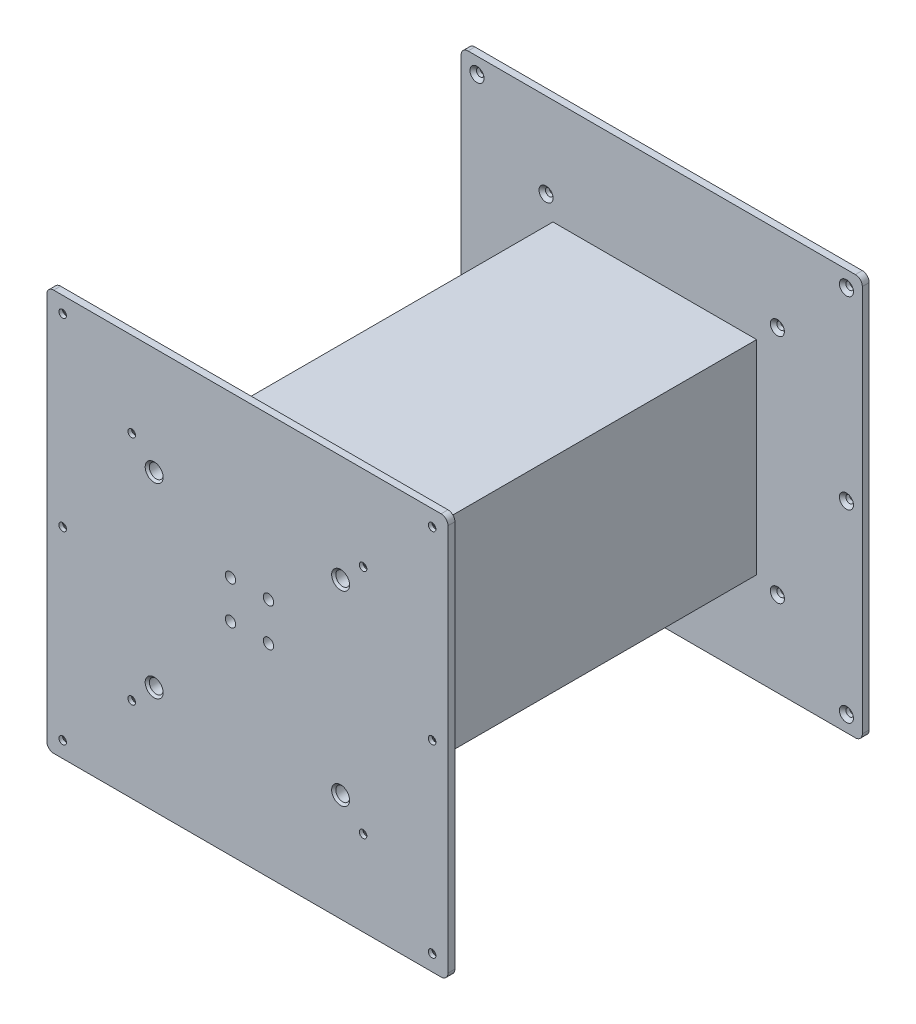
SolidWorks part; units mm, degrees
ref_plane "Front Plane" through (0, 0, 0) normal (0, 0, 1) x (1, 0, 0)
ref_plane "Top Plane" through (0, 0, 0) normal (0, 1, 0) x (1, 0, 0)
ref_plane "Right Plane" through (0, 0, 0) normal (1, 0, 0) x (0, 0, -1)
sketch "Sketch1" plane through (0, 0, 0) normal (0, 0, 1) x (1, 0, 0)
  line L1 (-147.574, 147.574) -> (147.574, 147.574)
  line L2 (-147.574, 147.574) -> (-147.574, -147.574)
  line L3 (-147.574, -147.574) -> (147.574, -147.574)
  line L4 (147.574, 147.574) -> (147.574, -147.574)
  line L5 (-147.574, 147.574) -> (147.574, -147.574) construction
  line L6 (-147.574, -147.574) -> (147.574, 147.574) construction
  point P0 (0, 0)
  dimension "D1" = 295.148
  dimension "D2" = 295.148
extrude "Boss-Extrude1" add sketch "Sketch1" along normal blind 5.08
sketch "Sketch2" plane through (0, 0, 5.08) normal (0, 0, 1) x (1, 0, 0)
  line L1 (-69.596, 69.596) -> (69.596, 69.596)
  line L2 (-69.596, 69.596) -> (-69.596, -69.596)
  line L3 (-69.596, -69.596) -> (69.596, -69.596)
  line L4 (69.596, 69.596) -> (69.596, -69.596)
  line L5 (-69.596, 69.596) -> (69.596, -69.596) construction
  line L6 (-69.596, -69.596) -> (69.596, 69.596) construction
  point P0 (0, 0)
  dimension "D1" = 139.192
  dimension "D2" = 139.192
extrude "Boss-Extrude2" add sketch "Sketch2" along normal blind 5.08
sketch "Sketch3" plane through (0, 0, 10.16) normal (0, 0, 1) x (1, 0, 0)
  line L1 (-74.93, 74.93) -> (74.93, 74.93)
  line L2 (-74.93, 74.93) -> (-74.93, -74.93)
  line L3 (-74.93, -74.93) -> (74.93, -74.93)
  line L4 (74.93, 74.93) -> (74.93, -74.93)
  line L5 (-74.93, 74.93) -> (74.93, -74.93) construction
  line L6 (-74.93, -74.93) -> (74.93, 74.93) construction
  point P0 (0, 0)
  dimension "D1" = 149.86
  dimension "D2" = 149.86
extrude "Boss-Extrude3" add sketch "Sketch3" along normal blind 294.64
sketch "Sketch4" plane through (0, 0, 304.8) normal (0, 0, 1) x (1, 0, 0)
  line L1 (147.574, -147.574) -> (-147.574, -147.574)
  line L2 (147.574, -147.574) -> (147.574, 147.574)
  line L3 (147.574, 147.574) -> (-147.574, 147.574)
  line L4 (-147.574, -147.574) -> (-147.574, 147.574)
  line L5 (147.574, -147.574) -> (-147.574, 147.574) construction
  line L6 (147.574, 147.574) -> (-147.574, -147.574) construction
  point P0 (0, 0)
extrude "Boss-Extrude4" add sketch "Sketch4" along normal blind 5.08
sketch "Sketch5" plane through (0, 0, 0) normal (0, 0, -1) x (-1, 0, 0)
  line L0 (147.574, -147.574) -> (-147.574, -147.574) construction
  line L1 (-147.574, -147.574) -> (-147.574, 147.574) construction
  line L2 (-147.574, 147.574) -> (147.574, 147.574) construction
  circle A0 centre (-135.89, 135.89) radius 2.794
  circle A1 centre (135.89, 135.89) radius 2.794
  circle A2 centre (135.89, -135.89) radius 2.794
  circle A3 centre (-135.89, -135.89) radius 2.794
  circle A4 centre (-135.89, 0) radius 2.794
  circle A5 centre (135.89, 0) radius 2.794
  circle A6 centre (-85.09, 85.09) radius 2.794
  circle A7 centre (85.09, 85.09) radius 2.794
  circle A8 centre (85.09, -85.09) radius 2.794
  circle A9 centre (-85.09, -85.09) radius 2.794
  dimension "D1" = 271.78
  dimension "D2" = 271.78
  dimension "D3" = 11.684
  dimension "D4" = 11.684
  dimension "D5" = 271.78
  dimension "D6" = 271.78
  dimension "D7" = 5.588
  dimension "D8" = 5.588
  dimension "D9" = 5.588
  dimension "D10" = 5.588
  dimension "D11" = 5.588
  dimension "D12" = 5.588
  dimension "D13" = 170.18
  dimension "D14" = 170.18
  dimension "D15" = 170.18
  dimension "D16" = 62.484
  dimension "D17" = 62.484
  dimension "D18" = 5.588
  dimension "D19" = 5.588
  dimension "D20" = 5.588
  dimension "D21" = 5.588
extrude "Cut-Extrude1" cut sketch "Sketch5" against normal through all
chamfer "Chamfer1" distance 2.38 angle 45 1 edges at (138.684, 135.89, 304.8)
chamfer "Chamfer2" distance 2.38 angle 45 19 edges at (138.684, 0, 5.08) (138.684, -135.89, 5.08) (87.884, -85.09, 5.08) (-133.096, -135.89, 5.08) (-82.296, -85.09, 5.08) (-133.096, 0, 5.08) (-133.096, 0, 304.8) (-133.096, -135.89, 304.8) (-82.296, -85.09, 304.8) (138.684, 135.89, 5.08) (87.884, 85.09, 5.08) (-82.296, 85.09, 5.08) (-133.096, 135.89, 5.08) (-82.296, 85.09, 304.8) (-133.096, 135.89, 304.8) (87.884, -85.09, 304.8) (138.684, -135.89, 304.8) (138.684, 0, 304.8) (87.884, 85.09, 304.8)
fillet "Fillet1" radius 5.08 1 edges at (147.574, 147.574, 2.54)
fillet "Fillet2" radius 5.08 7 edges at (147.574, 147.574, 307.34) (147.574, -147.574, 2.54) (147.574, -147.574, 307.34) (-147.574, -147.574, 2.54) (-147.574, -147.574, 307.34) (-147.574, 147.574, 307.34) (-147.574, 147.574, 2.54)
sketch "Sketch6" plane through (0, 0, 309.88) normal (0, 0, 1) x (1, 0, 0)
  line L0 (142.494, 147.574) -> (-142.494, 147.574) construction
  line L1 (-147.574, 142.494) -> (-147.574, -142.494) construction
  circle A0 centre (-68.58, -68.58) radius 5.08
  circle A1 centre (-68.58, 68.58) radius 5.08
  circle A2 centre (68.58, 68.58) radius 5.08
  circle A3 centre (68.58, -68.58) radius 5.08
  dimension "D1" = 137.16
  dimension "D2" = 137.16
  dimension "D3" = 137.16
  dimension "D4" = 78.994
  dimension "D5" = 10.16
  dimension "D6" = 10.16
  dimension "D7" = 10.16
  dimension "D8" = 10.16
  dimension "D9" = 78.994
extrude "Cut-Extrude3" cut sketch "Sketch6" against normal blind 35.56
chamfer "Chamfer3" distance 1.524 angle 45 4 edges at (73.66, 68.58, 309.88) (-63.5, -68.58, 309.88) (-63.5, 68.58, 309.88) (73.66, -68.58, 309.88)
sketch "Sketch7" plane through (0, 0, 0) normal (0, 0, -1) x (-1, 0, 0)
  line L0 (-142.494, 147.574) -> (142.494, 147.574) construction
  line L1 (-147.574, -142.494) -> (-147.574, 142.494) construction
  circle A0 centre (-53.34, 53.34) radius 5.08
  circle A1 centre (-53.34, -53.34) radius 5.08
  circle A2 centre (53.34, -53.34) radius 5.08
  circle A3 centre (53.34, 53.34) radius 5.08
  dimension "D1" = 106.68
  dimension "D2" = 106.68
  dimension "D3" = 106.68
  dimension "D4" = 94.234
  dimension "D5" = 94.234
  dimension "D6" = 10.16
  dimension "D7" = 10.16
  dimension "D8" = 10.16
  dimension "D9" = 10.16
extrude "Cut-Extrude4" cut sketch "Sketch7" against normal blind 35.56
chamfer "Chamfer5" distance 1.524 angle 45 4 edges at (48.26, -53.34, 0) (-58.42, -53.34, 0) (-58.42, 53.34, 0) (48.26, 53.34, 0)
sketch "Sketch8" plane through (0, 0, 309.88) normal (0, 0, 1) x (1, 0, 0)
  line L0 (142.494, 147.574) -> (-142.494, 147.574) construction
  line L1 (147.574, -142.494) -> (147.574, 142.494) construction
  circle A0 centre (15.494, 29.464) radius 3.81
  circle A1 centre (15.494, 1.524) radius 3.81
  circle A2 centre (-12.446, 1.524) radius 3.81
  circle A3 centre (-12.446, 29.464) radius 3.81
  dimension "D1" = 27.94
  dimension "D2" = 27.94
  dimension "D3" = 118.11
  dimension "D4" = 118.11
  dimension "D5" = 7.62
  dimension "D6" = 7.62
  dimension "D7" = 7.62
  dimension "D8" = 7.62
  dimension "D9" = 132.08
  dimension "D10" = 27.94
extrude "Cut-Extrude5" cut sketch "Sketch8" against normal blind 35.56
sketch "Sketch9" plane through (0, 0, 0) normal (0, 0, -1) x (-1, 0, 0)
  line L0 (-142.494, 147.574) -> (142.494, 147.574) construction
  line L1 (147.574, 142.494) -> (147.574, -142.494) construction
  circle A0 centre (15.494, 29.464) radius 3.81
  circle A1 centre (15.494, 1.524) radius 3.81
  circle A2 centre (-12.446, 29.464) radius 3.81
  circle A3 centre (-12.446, 1.524) radius 3.81
  dimension "D1" = 27.94
  dimension "D2" = 27.94
  dimension "D3" = 27.94
  dimension "D4" = 118.11
  dimension "D5" = 7.62
  dimension "D6" = 7.62
  dimension "D7" = 7.62
  dimension "D8" = 7.62
  dimension "D9" = 132.08
extrude "Cut-Extrude6" cut sketch "Sketch9" against normal blind 35.56
